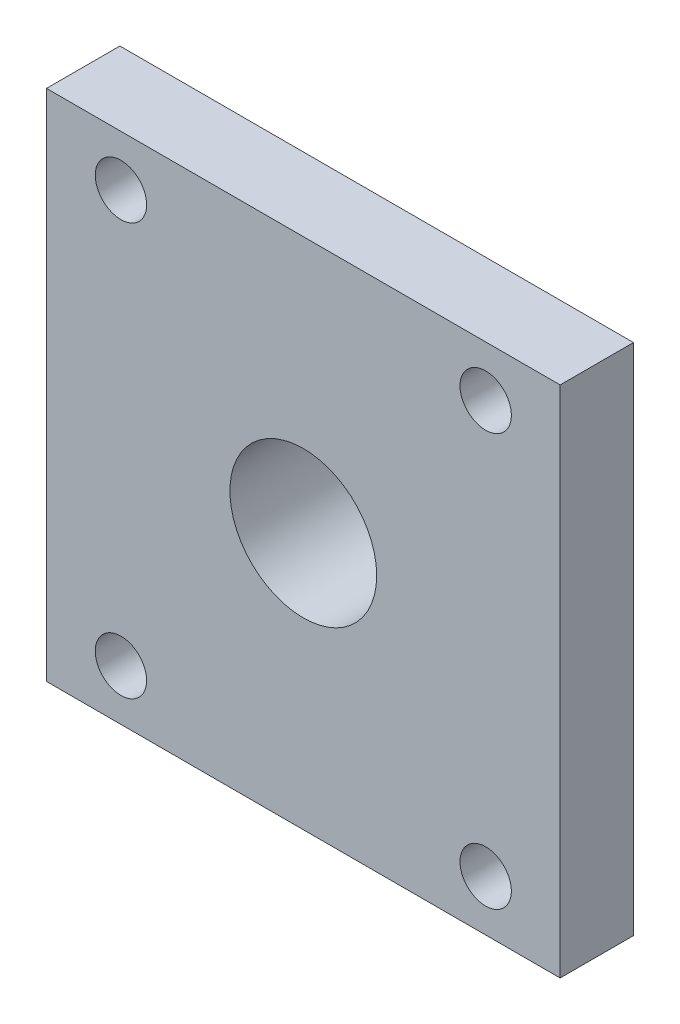
SolidWorks part; units mm, degrees
ref_plane "Front Plane" through (0, 0, 0) normal (0, 0, 1) x (1, 0, 0)
ref_plane "Top Plane" through (0, 0, 0) normal (0, 1, 0) x (1, 0, 0)
ref_plane "Right Plane" through (0, 0, 0) normal (1, 0, 0) x (0, 0, -1)
sketch "Sketch1" plane through (0, 0, 0) normal (0, 0, 1) x (1, 0, 0)
  line L1 (-35, 35) -> (35, 35)
  line L2 (-35, 35) -> (-35, -35)
  line L3 (-35, -35) -> (35, -35)
  line L4 (35, 35) -> (35, -35)
  line L5 (-35, 35) -> (35, -35) construction
  line L6 (-35, -35) -> (35, 35) construction
  point P0 (0, 0)
  dimension "D1" = 70
  dimension "D2" = 70
extrude "Boss-Extrude1" add sketch "Sketch1" along normal blind 10
sketch "Sketch2" plane through (0, 0, 10) normal (0, 0, 1) x (1, 0, 0)
  circle A0 centre (0, 0) radius 10
  dimension "D1" = 20
extrude "Cut-Extrude1" cut sketch "Sketch2" against normal blind 10
sketch "Sketch4" plane through (0, 0, 0) normal (0, 0, -1) x (-1, 0, 0)
  line L1 (-24.8556, 28.0793) -> (24.8556, 28.0793)
  line L2 (-24.8556, 28.0793) -> (-24.8556, -28.0793) construction
  line L3 (-24.8556, -28.0793) -> (24.8556, -28.0793)
  line L4 (24.8556, 28.0793) -> (24.8556, -28.0793)
  line L5 (-24.8556, 28.0793) -> (24.8556, -28.0793) construction
  line L6 (-24.8556, -28.0793) -> (24.8556, 28.0793) construction
  circle A0 centre (0, 0) radius 37.5 construction
  circle A1 centre (-24.8556, 28.0793) radius 3.5
  circle A2 centre (24.8556, 28.0793) radius 3.5
  circle A3 centre (24.8556, -28.0793) radius 3.5
  circle A4 centre (-24.8556, -28.0793) radius 3.5
  dimension "D1" = 75
  dimension "D2" = 7
  dimension "D3" = 7
  dimension "D4" = 7
  dimension "D5" = 7
extrude "Cut-Extrude2" cut sketch "Sketch4" against normal blind 35
sketch "Sketch5" plane through (0, 0, 0) normal (0, 0, -1) x (-1, 0, 0)
  circle A0 centre (0, 0) radius 10
  circle A1 centre (0, 0) radius 13.072
extrude "Boss-Extrude3" add sketch "Sketch5" along normal blind 15
